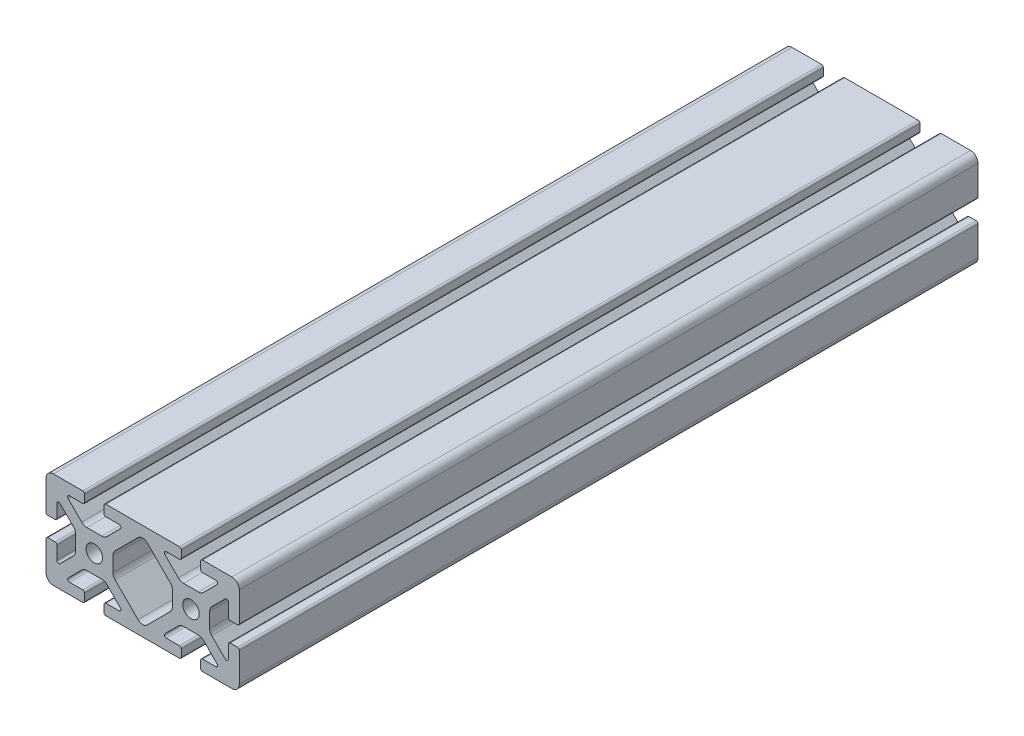
SolidWorks part; units mm, degrees
ref_plane "Front Plane" through (0, 0, 0) normal (0, 0, 1) x (1, 0, 0)
ref_plane "Top Plane" through (0, 0, 0) normal (0, 1, 0) x (1, 0, 0)
ref_plane "Right Plane" through (0, 0, 0) normal (1, 0, 0) x (0, 0, -1)
sketch "Sketch1" plane through (0, 0, 0) normal (0, 0, 1) x (1, 0, 0)
  line L2 (-39.878, 16.891) -> (-39.878, 4.7625)
  line L3 (-36.83, 19.939) -> (-24.7015, 19.939)
  line L4 (-23.9395, 19.177) -> (-23.9395, 16.2052)
  line L5 (-24.7015, 15.4432) -> (-30.1625, 15.4432)
  line L6 (-30.7013, 14.1424) -> (-25.133, 8.5741)
  line L7 (-34.0814, 10.7623) -> (-28.5131, 5.194)
  line L8 (-35.3822, 10.2235) -> (-35.3822, 4.7625)
  line L9 (-36.1442, 4.0005) -> (-39.116, 4.0005)
  line L11 (-23.0136, 7.6962) -> (-16.8644, 7.6962)
  line L12 (-27.6352, 3.0746) -> (-27.6352, -3.0746)
  line L13 (15.1765, 19.939) -> (-15.1765, 19.939)
  line L14 (-15.9385, 19.177) -> (-15.9385, 16.2052)
  line L15 (-15.1765, 15.4432) -> (-9.7155, 15.4432)
  line L16 (-12.2428, 3.0746) -> (-12.2428, -3.0746)
  line L17 (-9.1767, 14.1424) -> (-14.745, 8.5741)
  line L18 (-1.9047, 14.6543) -> (-11.3649, 5.194)
  line L19 (-36.1442, -4.0005) -> (-39.116, -4.0005)
  line L20 (-35.3822, -10.2235) -> (-35.3822, -4.7625)
  line L21 (-34.0814, -10.7623) -> (-28.5131, -5.194)
  line L22 (-30.7013, -14.1424) -> (-25.133, -8.5741)
  line L23 (-24.7015, -15.4432) -> (-30.1625, -15.4432)
  line L24 (-23.9395, -19.177) -> (-23.9395, -16.2052)
  line L25 (-36.83, -19.939) -> (-24.7015, -19.939)
  line L26 (-39.878, -16.891) -> (-39.878, -4.7625)
  line L27 (15.1765, -19.939) -> (-15.1765, -19.939)
  line L28 (-15.9385, -19.177) -> (-15.9385, -16.2052)
  line L29 (-15.1765, -15.4432) -> (-9.7155, -15.4432)
  line L30 (-9.1767, -14.1424) -> (-14.745, -8.5741)
  line L31 (-1.9047, -14.6543) -> (-11.3649, -5.194)
  line L32 (-23.0136, -7.6962) -> (-16.8644, -7.6962)
  line L34 (23.0136, -7.6962) -> (16.8644, -7.6962)
  line L35 (1.9047, -14.6543) -> (11.3649, -5.194)
  line L36 (9.1767, -14.1424) -> (14.745, -8.5741)
  line L37 (15.1765, -15.4432) -> (9.7155, -15.4432)
  line L38 (15.9385, -19.177) -> (15.9385, -16.2052)
  line L40 (39.878, -16.891) -> (39.878, -4.7625)
  line L41 (36.83, -19.939) -> (24.7015, -19.939)
  line L42 (23.9395, -19.177) -> (23.9395, -16.2052)
  line L43 (24.7015, -15.4432) -> (30.1625, -15.4432)
  line L44 (30.7013, -14.1424) -> (25.133, -8.5741)
  line L45 (34.0814, -10.7623) -> (28.5131, -5.194)
  line L46 (35.3822, -10.2235) -> (35.3822, -4.7625)
  line L47 (36.1442, -4.0005) -> (39.116, -4.0005)
  line L48 (1.9047, 14.6543) -> (11.3649, 5.194)
  line L49 (9.1767, 14.1424) -> (14.745, 8.5741)
  line L50 (12.2428, 3.0746) -> (12.2428, -3.0746)
  line L51 (15.1765, 15.4432) -> (9.7155, 15.4432)
  line L52 (15.9385, 19.177) -> (15.9385, 16.2052)
  line L53 (27.6352, 3.0746) -> (27.6352, -3.0746)
  line L54 (23.0136, 7.6962) -> (16.8644, 7.6962)
  line L55 (36.1442, 4.0005) -> (39.116, 4.0005)
  line L56 (35.3822, 10.2235) -> (35.3822, 4.7625)
  line L57 (34.0814, 10.7623) -> (28.5131, 5.194)
  line L58 (30.7013, 14.1424) -> (25.133, 8.5741)
  line L59 (24.7015, 15.4432) -> (30.1625, 15.4432)
  line L60 (23.9395, 19.177) -> (23.9395, 16.2052)
  line L61 (36.83, 19.939) -> (24.7015, 19.939)
  line L62 (39.878, 16.891) -> (39.878, 4.7625)
  circle A0 centre (-19.939, 0) radius 3.4036
  arc A1 (-39.878, 16.891) -> (-36.83, 19.939) centre (-36.83, 16.891) cw
  arc A2 (-34.0814, 10.7623) -> (-35.3822, 10.2235) centre (-34.6202, 10.2235) ccw
  arc A3 (-30.1625, 15.4432) -> (-30.7013, 14.1424) centre (-30.1625, 14.6812) ccw
  arc A4 (-24.7015, 19.939) -> (-23.9395, 19.177) centre (-24.7015, 19.177) cw
  arc A5 (-39.878, 4.7625) -> (-39.116, 4.0005) centre (-39.116, 4.7625) ccw
  arc A6 (-35.3822, 4.7625) -> (-36.1442, 4.0005) centre (-36.1442, 4.7625) cw
  arc A7 (-23.9395, 16.2052) -> (-24.7015, 15.4432) centre (-24.7015, 16.2052) cw
  arc A8 (-23.0136, 7.6962) -> (-25.133, 8.5741) centre (-23.0136, 10.6934) cw
  arc A9 (-27.6352, 3.0746) -> (-28.5131, 5.194) centre (-30.6324, 3.0746) ccw
  arc A10 (1.9047, 14.6543) -> (-1.9047, 14.6543) centre (0, 12.7496) ccw
  arc A11 (-1.9047, -14.6543) -> (1.9047, -14.6543) centre (0, -12.7496) ccw
  arc A12 (-15.1765, 19.939) -> (-15.9385, 19.177) centre (-15.1765, 19.177) ccw
  arc A13 (-15.9385, 16.2052) -> (-15.1765, 15.4432) centre (-15.1765, 16.2052) ccw
  arc A14 (-16.8644, 7.6962) -> (-14.745, 8.5741) centre (-16.8644, 10.6934) ccw
  arc A15 (-12.2428, 3.0746) -> (-11.3649, 5.194) centre (-9.2456, 3.0746) cw
  arc A16 (-9.7155, 15.4432) -> (-9.1767, 14.1424) centre (-9.7155, 14.6812) cw
  arc A17 (-27.6352, -3.0746) -> (-28.5131, -5.194) centre (-30.6324, -3.0746) cw
  arc A18 (-23.0136, -7.6962) -> (-25.133, -8.5741) centre (-23.0136, -10.6934) ccw
  arc A19 (-23.9395, -16.2052) -> (-24.7015, -15.4432) centre (-24.7015, -16.2052) ccw
  arc A20 (-35.3822, -4.7625) -> (-36.1442, -4.0005) centre (-36.1442, -4.7625) ccw
  arc A21 (-39.878, -4.7625) -> (-39.116, -4.0005) centre (-39.116, -4.7625) cw
  arc A22 (-24.7015, -19.939) -> (-23.9395, -19.177) centre (-24.7015, -19.177) ccw
  arc A23 (-30.1625, -15.4432) -> (-30.7013, -14.1424) centre (-30.1625, -14.6812) cw
  arc A24 (-34.0814, -10.7623) -> (-35.3822, -10.2235) centre (-34.6202, -10.2235) cw
  arc A25 (-39.878, -16.891) -> (-36.83, -19.939) centre (-36.83, -16.891) ccw
  arc A26 (-9.7155, -15.4432) -> (-9.1767, -14.1424) centre (-9.7155, -14.6812) ccw
  arc A27 (-15.1765, -19.939) -> (-15.9385, -19.177) centre (-15.1765, -19.177) cw
  arc A28 (-15.9385, -16.2052) -> (-15.1765, -15.4432) centre (-15.1765, -16.2052) cw
  arc A29 (-16.8644, -7.6962) -> (-14.745, -8.5741) centre (-16.8644, -10.6934) cw
  arc A30 (-12.2428, -3.0746) -> (-11.3649, -5.194) centre (-9.2456, -3.0746) ccw
  arc A31 (12.2428, -3.0746) -> (11.3649, -5.194) centre (9.2456, -3.0746) cw
  arc A32 (16.8644, -7.6962) -> (14.745, -8.5741) centre (16.8644, -10.6934) ccw
  arc A33 (15.9385, -16.2052) -> (15.1765, -15.4432) centre (15.1765, -16.2052) ccw
  arc A34 (15.1765, -19.939) -> (15.9385, -19.177) centre (15.1765, -19.177) ccw
  arc A35 (9.7155, -15.4432) -> (9.1767, -14.1424) centre (9.7155, -14.6812) cw
  arc A36 (39.878, -16.891) -> (36.83, -19.939) centre (36.83, -16.891) cw
  arc A37 (34.0814, -10.7623) -> (35.3822, -10.2235) centre (34.6202, -10.2235) ccw
  arc A38 (30.1625, -15.4432) -> (30.7013, -14.1424) centre (30.1625, -14.6812) ccw
  arc A39 (24.7015, -19.939) -> (23.9395, -19.177) centre (24.7015, -19.177) cw
  arc A40 (39.878, -4.7625) -> (39.116, -4.0005) centre (39.116, -4.7625) ccw
  arc A41 (35.3822, -4.7625) -> (36.1442, -4.0005) centre (36.1442, -4.7625) cw
  arc A42 (23.9395, -16.2052) -> (24.7015, -15.4432) centre (24.7015, -16.2052) cw
  arc A43 (23.0136, -7.6962) -> (25.133, -8.5741) centre (23.0136, -10.6934) cw
  arc A44 (27.6352, -3.0746) -> (28.5131, -5.194) centre (30.6324, -3.0746) ccw
  arc A45 (9.7155, 15.4432) -> (9.1767, 14.1424) centre (9.7155, 14.6812) ccw
  arc A46 (12.2428, 3.0746) -> (11.3649, 5.194) centre (9.2456, 3.0746) ccw
  arc A47 (16.8644, 7.6962) -> (14.745, 8.5741) centre (16.8644, 10.6934) cw
  arc A48 (15.9385, 16.2052) -> (15.1765, 15.4432) centre (15.1765, 16.2052) cw
  arc A49 (15.1765, 19.939) -> (15.9385, 19.177) centre (15.1765, 19.177) cw
  arc A50 (27.6352, 3.0746) -> (28.5131, 5.194) centre (30.6324, 3.0746) cw
  arc A51 (23.0136, 7.6962) -> (25.133, 8.5741) centre (23.0136, 10.6934) ccw
  arc A52 (23.9395, 16.2052) -> (24.7015, 15.4432) centre (24.7015, 16.2052) ccw
  arc A53 (35.3822, 4.7625) -> (36.1442, 4.0005) centre (36.1442, 4.7625) ccw
  arc A54 (39.878, 4.7625) -> (39.116, 4.0005) centre (39.116, 4.7625) cw
  arc A55 (24.7015, 19.939) -> (23.9395, 19.177) centre (24.7015, 19.177) ccw
  arc A56 (30.1625, 15.4432) -> (30.7013, 14.1424) centre (30.1625, 14.6812) cw
  arc A57 (34.0814, 10.7623) -> (35.3822, 10.2235) centre (34.6202, 10.2235) cw
  arc A58 (39.878, 16.891) -> (36.83, 19.939) centre (36.83, 16.891) ccw
  circle A59 centre (19.939, 0) radius 3.4036
  point P185 (19.939, 7.6962)
extrude "Boss-Extrude1" add sketch "Sketch1" along normal mid plane 304.8
